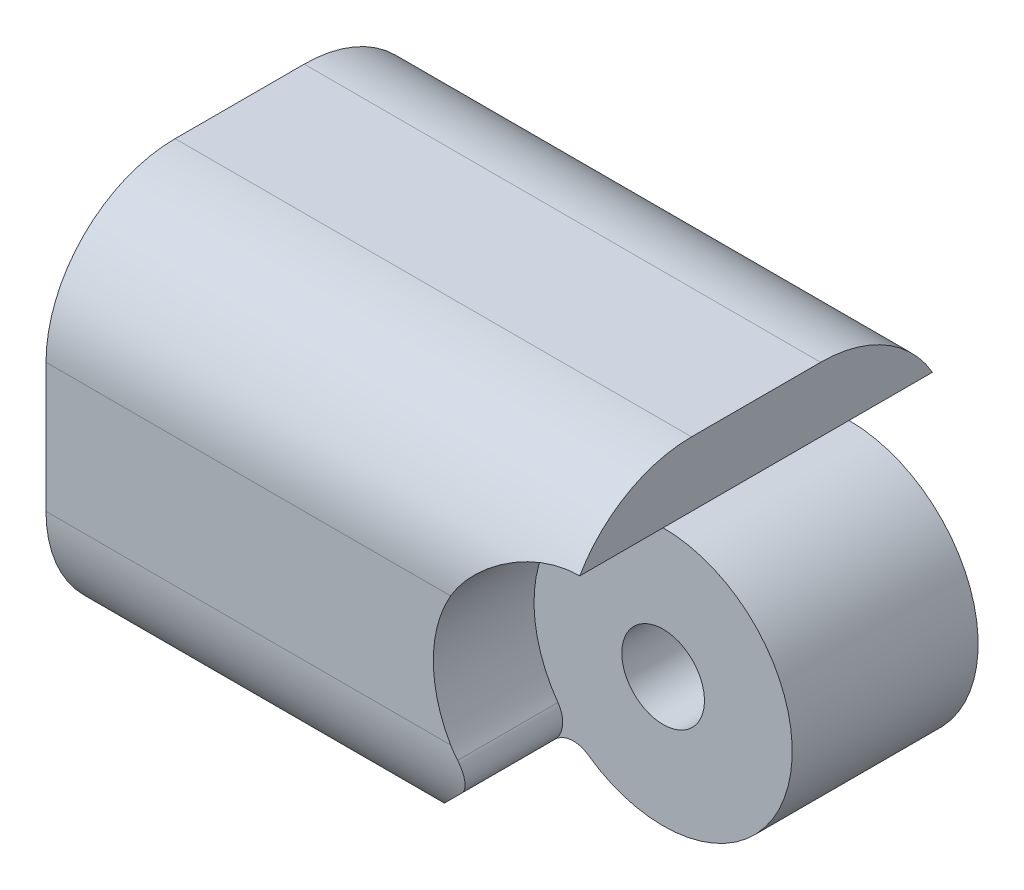
SolidWorks part; units mm, degrees
ref_plane "Front Plane" through (0, 0, 0) normal (0, 0, 1) x (1, 0, 0)
ref_plane "Top Plane" through (0, 0, 0) normal (0, 1, 0) x (1, 0, 0)
ref_plane "Right Plane" through (0, 0, 0) normal (1, 0, 0) x (0, 0, -1)
sketch "Sketch1" plane through (0, 0, 0) normal (0, 0, 1) x (1, 0, 0)
  line L0 (10, 5) -> (10, 7.5)
  line L1 (-10, 7.5) -> (10, 7.5)
  line L2 (-10, 7.5) -> (-10, -7.5)
  line L3 (-10, -7.5) -> (10, -7.5)
  line L5 (10, -5) -> (10, -7.5)
  arc A1 (10, -5) -> (10, 5) centre (10, 0) ccw
  circle A2 centre (10, 0) radius 1.6
  point P0 (0, 0)
  point P10 (0, 0)
  point P11 (0, 0)
  dimension "D3" = 3.2
  dimension "D6" = 10
  dimension "D1" = 20
  dimension "D2" = 15
  dimension "D4" = 10
  dimension "D5" = 7.5
  dimension "D7" = 2.5
extrude "Boss-Extrude1" add sketch "Sketch1" along normal blind 7.5
sketch "Sketch2" plane through (0, 0, 7.5) normal (0, 0, 1) x (1, 0, 0)
  line L0 (-10, 7.5) -> (-10, -7.5) construction
  circle A0 centre (-10, 0) radius 1.6
  circle A1 centre (10, 0) radius 1.6 construction
  circle A2 centre (-10, 0) radius 5.075
  dimension "D1" = 10.15
extrude "Cut-Extrude1" cut sketch "Sketch2" against normal blind 3.75
fillet "Fillet1" radius 5 2 edges at (0, -7.5, 0) (0, 7.5, 0)
sketch "Sketch3" plane through (0, 0, 0) normal (0, 0, -1) x (-1, 0, 0)
  circle A0 centre (-10, 0) radius 5
extrude "Cut-Extrude2" cut sketch "Sketch3" against normal blind 3.9
sketch "Sketch5" plane through (0, 0, 0) normal (0, 0, -1) x (-1, 0, 0)
  line L0 (-6.4645, -3.5355) -> (-2.5, -7.5)
  line L1 (10, -7.5) -> (-10, -7.5) construction
  line L2 (-2.5, -7.5) -> (-10, -7.5)
  line L3 (-10, -7.5) -> (-10, -5)
  arc A0 (-10, -5) -> (-6.4645, -3.5355) centre (-10, 0) ccw
  dimension "D2" = 2.5
  dimension "D1" = 7.5
  dimension "D3" = 5.6066
extrude "Cut-Extrude5" cut sketch "Sketch5" against normal through all
fillet "Fillet2" radius 1 1 edges at (6.4645, -3.5355, 2.0042)
mirror "Mirror2" about plane through (10, 0, 7.5) normal (0, 0, 1) of bodies 107 104
fillet "Fillet3" radius 1 1 edges at (6.4645, -3.5355, 7.5)
